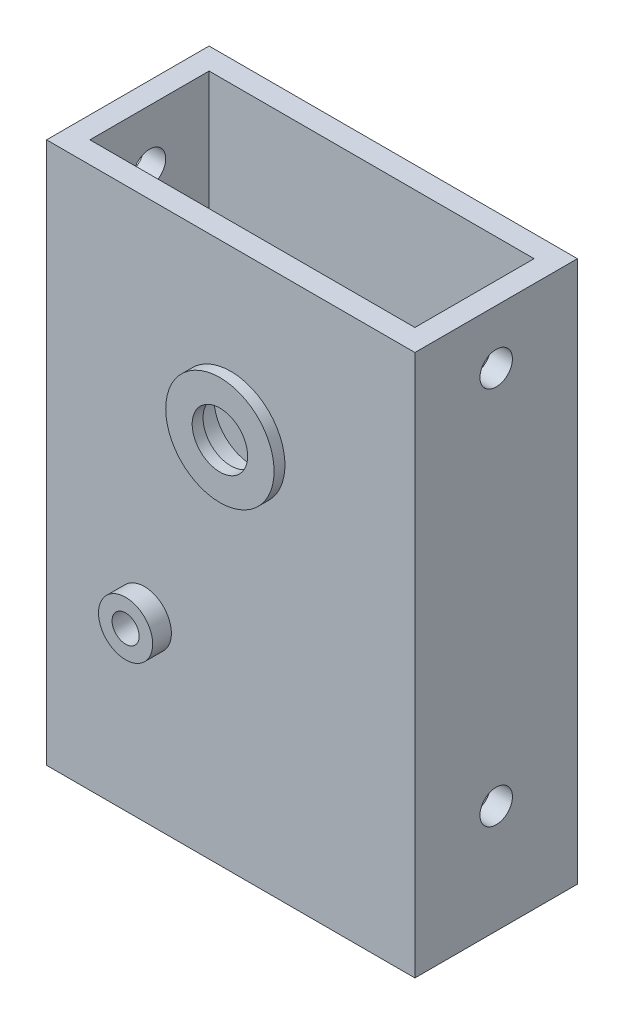
SolidWorks part; units mm, degrees
ref_plane "Front" through (0, 0, 0) normal (0, 0, 1) x (1, 0, 0)
ref_plane "Top" through (0, 0, 0) normal (0, 1, 0) x (1, 0, 0)
ref_plane "Right" through (0, 0, 0) normal (1, 0, 0) x (0, 0, -1)
sketch "Sketch1" plane through (0, 0, 0) normal (0, 1, 0) x (1, 0, 0)
  line L0 (-5.08, -5.08) -> (-5.08, 33.02)
  line L1 (0, 0) -> (76.2, 0)
  line L2 (0, 0) -> (0, 27.94)
  line L3 (0, 27.94) -> (76.2, 27.94)
  line L4 (76.2, 0) -> (76.2, 27.94)
  line L5 (-5.08, 33.02) -> (81.28, 33.02)
  line L6 (81.28, -5.08) -> (81.28, 33.02)
  line L7 (-5.08, -5.08) -> (81.28, -5.08)
  dimension "D2" = 76.2
  dimension "D3" = 27.94
  dimension "D1" = 5.08
extrude "Boss-Extrude1" add sketch "Sketch1" along normal blind 127
sketch "Sketch2" plane through (0, 0, 5.08) normal (0, 0, 1) x (1, 0, 0)
  line L0 (38.1, 127) -> (38.1, 0) construction
  line L1 (-5.08, 127) -> (81.28, 127) construction
  line L2 (-5.08, 0) -> (81.28, 0) construction
  line L3 (17.8334, 41.4281) -> (5.4164, 77.7165) construction
  line L4 (5.4164, 77.7165) -> (38.1, 88.9) construction
  circle A0 centre (38.1, 88.9) radius 9
  circle A1 centre (17.8334, 41.4281) radius 3.175
  circle A2 centre (38.1, 88.9) radius 10.2489 construction
  circle A3 centre (38.1, 88.9) radius 34.925 construction
  point P11 (0, 0)
  dimension "D1" = 18
  dimension "D5" = 20.4978
  dimension "D7" = 6.35
  dimension "D2" = 69.85
  dimension "D6" = 38.1
  dimension "D3" = 34.544
  dimension "D4" = 38.354
  dimension "D8" = 20.2666
extrude "Cut-Extrude1" cut sketch "Sketch2" against normal through all
sketch "Sketch3" plane through (81.28, 0, 0) normal (1, 0, 0) x (0, 0, -1)
  line L0 (13.97, 127) -> (13.97, 0) construction
  line L1 (-5.08, 127) -> (33.02, 127) construction
  line L2 (-5.08, 0) -> (33.02, 0) construction
  circle A0 centre (13.97, 114.3) radius 3.81
  circle A1 centre (13.97, 25.4) radius 3.81
  dimension "D1" = 7.62
  dimension "D3" = 12.7
  dimension "D4" = 25.4
extrude "Cut-Extrude2" cut sketch "Sketch3" against normal through all both and the other way through all
sketch "Sketch4" plane through (0, 0, -33.02) normal (0, 0, -1) x (-1, 0, 0)
  circle A0 centre (-17.8334, 41.4281) radius 6.35
  circle A1 centre (-17.8334, 41.4281) radius 3.175 construction
  circle A2 centre (-17.8334, 41.4281) radius 3.175
  dimension "D1" = 12.7
  dimension "D2" = 6.35
extrude "Boss-Extrude2" add sketch "Sketch4" along normal blind 4.385
sketch "Sketch5" plane through (0, 0, 5.08) normal (0, 0, 1) x (1, 0, 0)
  circle A0 centre (17.8334, 41.4281) radius 6.35
  circle A1 centre (17.8334, 41.4281) radius 3.175
  dimension "D1" = 6.35
  dimension "D2" = 12.7
extrude "Boss-Extrude3" add sketch "Sketch5" along normal blind 4.385
sketch "Sketch6" plane through (0, 0, 5.08) normal (0, 0, 1) x (1, 0, 0)
  circle A0 centre (38.1, 88.9) radius 12.7
  circle A1 centre (38.1, 88.9) radius 6.5
  dimension "D1" = 13
  dimension "D2" = 25.4
extrude "Boss-Extrude4" add sketch "Sketch6" along normal blind 2.54
sketch "Sketch7" plane through (0, 0, -33.02) normal (0, 0, -1) x (-1, 0, 0)
  circle A0 centre (-38.1, 88.9) radius 12.7
  circle A1 centre (-38.1, 88.9) radius 6.5
  circle A2 centre (-38.1, 88.9) radius 9 construction
  dimension "D1" = 25.4
  dimension "D2" = 13
extrude "Boss-Extrude5" add sketch "Sketch7" along normal blind 2.54
